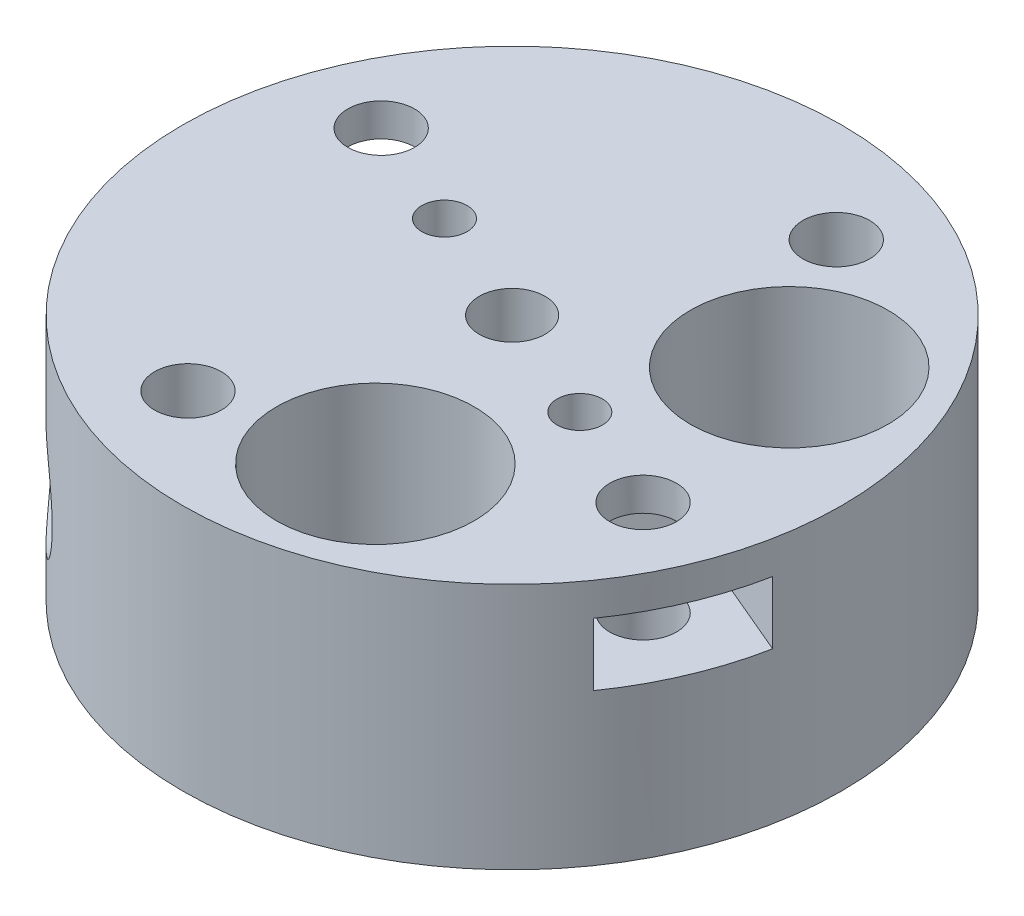
SolidWorks part; units mm, degrees
ref_plane "Front Plane" through (0, 0, 0) normal (0, 0, 1) x (1, 0, 0)
ref_plane "Top Plane" through (0, 0, 0) normal (0, 1, 0) x (1, 0, 0)
ref_plane "Right Plane" through (0, 0, 0) normal (1, 0, 0) x (0, 0, -1)
sketch "Sketch1" plane through (0, 0, 0) normal (0, 1, 0) x (1, 0, 0)
  circle A0 centre (0, 0) radius 20
  dimension "D1" = 40
extrude "Boss-Extrude1" add sketch "Sketch1" along normal mid plane 15
sketch "Sketch4" plane through (0, -7.5, 0) normal (0, -1, 0) x (1, 0, 0)
  circle A0 centre (0, 0) radius 5.125
  dimension "D1" = 10.25
extrude "Cut-Extrude2" cut sketch "Sketch4" against normal offset from surface (12.15 mm away) 2.85 up to face at (0, 7.5, 20)
sketch "Sketch5" plane through (0, 7.5, 0) normal (0, 1, 0) x (1, 0, 0)
  circle A0 centre (0, 0) radius 2
  dimension "D1" = 4
extrude "Cut-Extrude3" cut sketch "Sketch5" against normal through all both and the other way through all
sketch "Sketch2" plane through (0, 7.5, 0) normal (0, 1, 0) x (1, 0, 0)
  line L0 (0, 0) -> (0, 20) construction
  line L1 (0, 0) -> (-13.8076, 5.861) construction
  circle A0 centre (0, 0) radius 20 construction
  circle A1 centre (-13.8076, 5.861) radius 2.025
  dimension "D1" = 4.05
  dimension "D2" = 15
  dimension "D3" = 67
extrude "Cut-Extrude1" cut sketch "Sketch2" against normal through all
pattern_circular "CirPattern1" count 4 over 360 about axis through (0, 0, 0) along (0, 1, 0) of "Cut-Extrude1"
sketch "Sketch6" plane through (0, 0, 0) normal (0, 0, 1) x (1, 0, 0)
  line L0 (0, 7.5) -> (0, -7.5) construction
  line L1 (20, 7.5) -> (-20, 7.5) construction
  line L2 (-20, -7.5) -> (20, -7.5) construction
  line L3 (-20, 4.65) -> (20, 4.65) construction
  line L4 (-20, 7.5) -> (-20, -7.5) construction
  line L5 (20, -7.5) -> (20, 7.5) construction
  circle A0 centre (0, -1.35) radius 1.525
  dimension "D1" = 3.05
  dimension "D2" = 2.85
  dimension "D3" = 6
extrude "Cut-Extrude4" cut sketch "Sketch6" against normal through all
sketch "Sketch7" plane through (0, 0, 0) normal (0, 0, 1) x (1, 0, 0)
  circle A0 centre (0, -1.35) radius 3.25
  dimension "D1" = 6.5
extrude "Cut-Extrude5" cut sketch "Sketch7" along normal blind 8 from offset 20 offset against normal yes
sketch "Sketch9" plane through (0, 0, 0) normal (0, 0, 1) x (1, 0, 0)
  line L0 (20, -7.5) -> (20, 7.5) construction
  line L1 (0, -4.9873) -> (3.15, -3.1687) construction
  line L2 (3.15, -3.1687) -> (3.15, 0.4687)
  line L3 (3.15, 0.4687) -> (0, 2.2873)
  line L4 (0, 2.2873) -> (-3.15, 0.4687)
  line L5 (-3.15, 0.4687) -> (-3.15, -3.1687)
  line L6 (-3.15, -3.1687) -> (0, -4.9873) construction
  line L7 (3.15, -3.1687) -> (-3.15, -3.1687) construction
  line L8 (3.15, -3.1687) -> (3.15, -7.6851)
  line L9 (-3.15, -3.1687) -> (-3.15, -7.6851)
  line L10 (3.15, -7.6851) -> (-3.15, -7.6851)
  circle A0 centre (0, -1.35) radius 3.15 construction
  dimension "D1" = 6.3
extrude "Cut-Extrude11" cut sketch "Sketch9" against normal blind 2.9 from offset 6.5 offset against normal yes
pattern_circular "CirPattern2" count 2 every 135 about axis through (0, 0, 0) along (0, 1, 0) of "Cut-Extrude4", "Cut-Extrude5", "Cut-Extrude11"
sketch "Sketch8" plane through (0, 0, 0) normal (0, 1, 0) x (1, 0, 0)
  line L0 (0, 0) -> (-13.8076, 5.861) construction
  line L1 (-9.3965, 3.9886) -> (-9.9805, 8.7449)
  line L2 (-9.9805, 8.7449) -> (-14.3916, 10.6173)
  line L3 (-14.3916, 10.6173) -> (-18.2186, 7.7334) construction
  line L4 (-18.2186, 7.7334) -> (-17.6346, 2.9771) construction
  line L5 (-17.6346, 2.9771) -> (-13.2236, 1.1047)
  line L6 (-13.2236, 1.1047) -> (-9.3965, 3.9886)
  line L7 (-14.3916, 10.6173) -> (-17.6346, 2.9771) construction
  line L8 (-14.3916, 10.6173) -> (-19.5699, 12.8153)
  line L9 (-17.6346, 2.9771) -> (-22.813, 5.1751)
  line L10 (-19.5699, 12.8153) -> (-22.813, 5.1751)
  circle A0 centre (-13.8076, 5.861) radius 4.15 construction
  dimension "D1" = 8.3
extrude "Cut-Extrude7" cut sketch "Sketch8" against normal blind 3.8 from offset 5.5
pattern_circular "CirPattern3" count 2 over 360 about axis through (0, 0, 0) along (0, 1, 0) of "Cut-Extrude7"
sketch "Sketch10" plane through (0, 7.5, 0) normal (0, 1, 0) x (1, 0, 0)
  line L0 (0, 0) -> (0, -20) construction
  line L1 (0, 0) -> (3.6546, -11.9538) construction
  circle A0 centre (0, 0) radius 20 construction
  circle A1 centre (3.6546, -11.9538) radius 6
  dimension "D1" = 12
  dimension "D2" = 17
  dimension "D3" = 12.5
extrude "Cut-Extrude12" cut sketch "Sketch10" against normal through all both and the other way through all
pattern_circular "CirPattern4" count 2 every 100 about axis through (0, 7.5, 0) along (0, 1, 0) of "Cut-Extrude12"
sketch "Sketch11" plane through (0, 7.5, 0) normal (0, 1, 0) x (1, 0, 0)
  line L0 (0, 0) -> (13.8076, -5.861) construction
  circle A0 centre (7.1339, -3.0282) radius 1.375
  circle A1 centre (0, 0) radius 2 construction
  dimension "D1" = 2.75
  dimension "D2" = 7.75
extrude "Cut-Extrude13" cut sketch "Sketch11" against normal through all both and the other way through all
sketch "Sketch13" plane through (0, -7.5, 0) normal (0, -1, 0) x (-1, 0, 0)
  circle A0 centre (-7.1339, -3.0282) radius 2.375
  dimension "D1" = 4.75
extrude "Cut-Extrude24" cut sketch "Sketch13" against normal offset from surface (12 mm away) 3 up to face at (7.1339, 7.5, 4.4032)
pattern_circular "CirPattern5" count 2 over 360 about axis through (0, 0, 0) along (0, 1, 0) of "Cut-Extrude13", "Cut-Extrude24"
